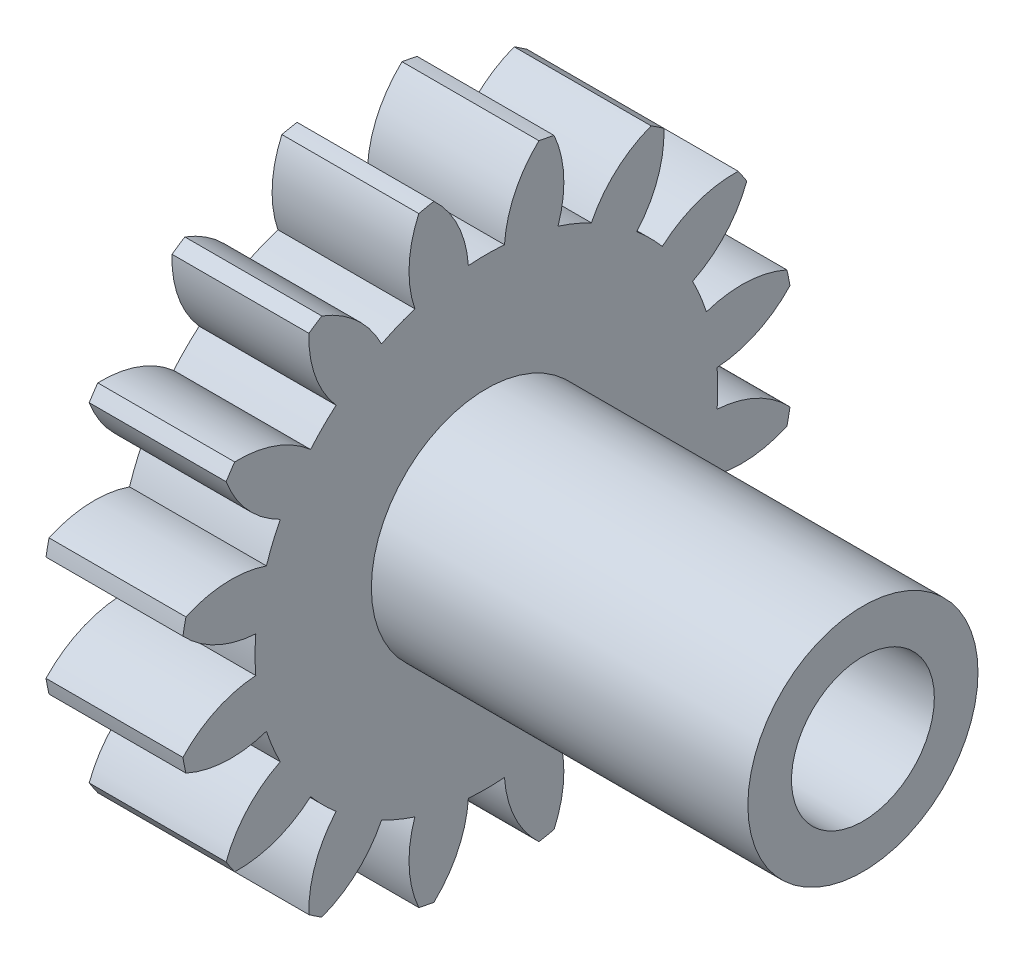
SolidWorks part; units mm, degrees
ref_plane "Plane1" through (0, 0, 0) normal (0, 0, 1) x (1, 0, 0)
ref_plane "Plane2" through (0, 0, 0) normal (0, 1, 0) x (1, 0, 0)
ref_plane "Plane3" through (0, 0, 0) normal (1, 0, 0) x (0, 0, -1)
sketch "HoldingSke" plane through (0, 0, 0) normal (0, 1, 0) x (1, 0, 0)
  line L0 (0, 0) -> (488.3209, -140.0238)
  line L1 (-15, 0) -> (100, 0) construction
  line L2 (0, 0) -> (-2.1039, 2.3779)
  line L3 (0, 0) -> (-11.863, 4.5341)
  line L4 (0, 0) -> (8.3015, 2.3804)
  line L5 (0, 0) -> (-47.5972, -17.7524)
  line L6 (0, 0) -> (-4.2111, -2.8413)
  line L7 (-2.1039, 2.3779) -> (8.8308, 51.9871)
  line L8 (-76.2, 54.61) -> (-74.168, 54.61)
  line L9 (-71.009, 38.7566) -> (-53.1078, 45.2721)
  line L10 (-76.2, 71.12) -> (104.1128, 71.12)
  line L11 (0, 0) -> (-5.08, 0)
  line L12 (-76.2, 101.6) -> (-76.1492, 101.6)
  line L13 (24.9733, 27.94) -> (52.9518, 28.4284)
  line L14 (24.9733, 27.94) -> (25.0241, 27.9398)
  line L15 (24.9733, 27.94) -> (100.4021, 29.52)
  circle A0 centre (0, 0) radius 0.9995
  circle A1 centre (0, 0) radius 8.5852
  circle A2 centre (0, 0) radius 38.1
  circle A3 centre (0, 0) radius 0.9995
  dimension "MHD" = 17.1704
  dimension "Hub_dia" = 76.2
  dimension "Bore" = 1.999
  dimension "MBD" = 1.999
  dimension "Num_teeth" = 16
  dimension "Pitch" = 508
  dimension "Overall_len" = 50.8
  dimension "Show_teeth" = 16
  dimension "Thickness" = 5.08
  dimension "OAL" = 50.8001
  dimension "T_dim" = 2.032
  dimension "Ap" = 20
  dimension "H" = 19.05
  dimension "Pitch_radius" = 180.3128
  dimension "Width" = 5.08
  dimension "Backlash" = 0.0508
  dimension "Addendum_fac" = 1
  dimension "Dedendum_fac" = 1.2
  dimension "Clearance_fac" = 0.2
  dimension "Dedendum_add" = 0.0508
sketch "BasProSke" plane through (0, 0, 0) normal (0, 1, 0) x (1, 0, 0)
  line L0 (-10, 0) -> (60, 0) construction
  line L1 (0, 0) -> (0, 11.43)
  line L2 (0, 0) -> (5.08, 0)
  line L3 (5.08, 0) -> (5.08, 11.43)
  line L4 (5.08, 11.43) -> (0, 11.43)
  dimension "Thickness" = 5.08
  dimension "Diameter" = 22.86
revolve "Base-Revolve" add sketch "BasProSke" angle 360 about L0
sketch "TooCutSke" plane through (0, 0, 0) normal (1, 0, 0) x (0, 0, -1)
  line L1 (0, 0) -> (0, 107) construction
  line L2 (0, 0) -> (-1.0847, 10.1019) construction
  line L3 (0, 0) -> (-3.9484, 19.85) construction
  line L4 (-1.0847, 10.1019) -> (-1.9742, 9.925) construction
  arc A0 (0.6699, 8.559) -> (-0.6699, 8.559) centre (0, 0) ccw
  arc A1 (1.9714, 11.2845) -> (-1.9714, 11.2845) centre (0, 0) ccw
  circle A2 centre (0, 0) radius 10.16 construction
  circle A3 centre (0, 0) radius 9.5473 construction
  arc A4 (-0.6699, 8.559) -> (-1.9714, 11.2845) centre (-4.7253, 8.2959) ccw
  arc A5 (1.9714, 11.2845) -> (0.6699, 8.559) centre (4.7253, 8.2959) ccw
  dimension "Root_dia" = 17.1704
  dimension "Overcut_dia" = 22.9108
  dimension "Pitch_dia" = 20.32
  dimension "Base_dia" = 19.0946
  dimension "Flank_rad" = 4.064
  dimension "Half_ang" = 11.25
  dimension "Half_CT" = 0.907
extrude "ToothCut" cut sketch "TooCutSke" along normal through all
fillet "Breaks" [suppressed] radius 0.0254
fillet "RootFillets" [suppressed] radius 0.3048
pattern_circular "TeethCuts" count 16 every 22.5 about axis through (-10, 0, 0) along (1, 0, 0) of "ToothCut", "RootFillets", "Breaks"
sketch "HubNeaOneSke" plane through (0, 0, 0) normal (-1, 0, 0) x (0, 0, 1)
  circle A0 centre (0, 0) radius 8.5852
  dimension "Diameter" = 17.1704
extrude "HubNearOne" [suppressed] add sketch "HubNeaOneSke" along normal blind 45.7201
sketch "HubNeaBotSke" plane through (0, 0, 0) normal (-1, 0, 0) x (0, 0, 1)
  circle A0 centre (0, 0) radius 8.5852
  dimension "Diameter" = 17.1704
extrude "HubNearBoth" [suppressed] add sketch "HubNeaBotSke" along normal blind 22.86
ref_plane "FarPln" through (5.08, 0, 0) normal (1, 0, 0) x (0, 0, -1)
sketch "HubFarSke" plane through (5.08, 0, 0) normal (1, 0, 0) x (0, 0, -1)
  circle A0 centre (0, 0) radius 8.5852
  dimension "Diameter" = 17.1704
extrude "HubFar" [suppressed] add sketch "HubFarSke" along normal blind 22.86
sketch "BorSke" plane through (0, 0, 0) normal (1, 0, 0) x (0, 0, -1)
  circle A0 centre (0, 0) radius 0.9995
  dimension "Diameter" = 1.999
extrude "Bore" cut sketch "BorSke" along normal mid plane 101.6001
sketch "KeySke" plane through (0, 0, 0) normal (1, 0, 0) x (0, 0, -1)
  line L0 (-0.127, 0) -> (-0.127, 1.0325)
  line L1 (-0.127, 1.0325) -> (0.127, 1.0325)
  line L2 (0.127, 1.0325) -> (0.127, 0)
  line L3 (0, 0) -> (0, 34) construction
  line L4 (-0.127, 0) -> (0.127, 0)
  dimension "Offset" = 1.0325
  dimension "Width" = 0.254
extrude "Keyway" [suppressed] cut sketch "KeySke" along normal mid plane 101.6001
pattern_circular "Keyway2" [suppressed] count 2 every 90 about axis through (-10, 0, 0) along (1, 0, 0)
sketch "Sketch1" plane through (5.08, 0, 0) normal (1, 0, 0) x (0, 0, -1)
  circle A0 centre (0, 0) radius 0.9995
extrude "Boss-Extrude1" add sketch "Sketch1" against normal up to surface (5.08 mm away) up to face at (0, 0, -0.9995)
sketch "Sketch2" plane through (5.08, 0, 0) normal (1, 0, 0) x (0, 0, -1)
  circle A0 centre (0, 0) radius 4.27
  dimension "D1" = 8.54
extrude "Boss-Extrude2" add sketch "Sketch2" along normal blind 13.97
sketch "Sketch3" plane through (19.05, 0, 0) normal (1, 0, 0) x (0, 0, -1)
  circle A0 centre (0, 0) radius 2.65
  dimension "D1" = 5.3
extrude "Cut-Extrude1" cut sketch "Sketch3" against normal blind 3.81
equation "' \"Pitch@HoldingSke\" = 4"
equation "' \"Num_teeth@HoldingSke\" = 12"
equation "' \"Ap@HoldingSke\" =  20"
equation "' \"Ap@HoldingSke\" = 20"
equation "' \"Width@HoldingSke\" = 0.5"
equation "' \"Hub_dia@HoldingSke\"= 1"
equation "' \"Hub_dia@HoldingSke\" = 1"
equation "' \"Overall_len@HoldingSke\" = 1.0"
equation "' \"Bore@HoldingSke\" = 0.75"
equation "' \"T_dim@HoldingSke\" = 0.85"
equation "' \"Width@KeySke\" = 0.25"
equation "' \"Show_teeth@HoldingSke\" = 13"
equation "' \"Backlash@HoldingSke\" = 0.009"
equation "' \"Addendum_fac@HoldingSke\" = 1.0"
equation "' \"Dedendum_fac@HoldingSke\" = 1.25"
equation "' \"Dedendum_add@HoldingSke\" = 0.00005"
equation "' \"Clearance_fac@HoldingSke\" = 0.25"
equation "' \"Pitch@HoldingSke\" = 0.5"
equation "' \"Num_teeth@HoldingSke\" = 23"
equation "' \"Show_teeth@HoldingSke\" = 23"
equation "' \"Backlash@HoldingSke\" = 0.0375"
equation "\"Overcut_dia@TooCutSke\" = (\"Num_teeth@HoldingSke\" + 2 * \"Addendum_fac@HoldingSke\") / \"Pitch@HoldingSke\" + 0.002"
equation "\"Pitch_dia@TooCutSke\" = \"Num_teeth@HoldingSke\" / \"Pitch@HoldingSke\""
equation "\"Base_dia@TooCutSke\" = \"Num_teeth@HoldingSke\" / \"Pitch@HoldingSke\" * cos((\"Ap@HoldingSke\"  * 3.14159265 / 180))"
equation "\"Root_dia@TooCutSke\" = (\"Num_teeth@HoldingSke\" + 2) / \"Pitch@HoldingSke\" - 2 * (\"Addendum_fac@HoldingSke\" + \"Dedendum_fac@HoldingSke\") / \"Pitch@HoldingSke\" - \"Dedendum_add@HoldingSke\" * 2"
equation "\"Half_ang@TooCutSke\" = 180 / \"Num_teeth@HoldingSke\""
equation "\"Half_CT@TooCutSke\" = \"Num_teeth@HoldingSke\" / \"Pitch@HoldingSke\" * sin((3.14159265 / 2 / \"Num_teeth@HoldingSke\")) / 2 - 7 * \"Backlash@HoldingSke\" / 4"
equation "\"Flank_rad@TooCutSke\" = \"Num_teeth@HoldingSke\" / \"Pitch@HoldingSke\" / 5"
equation "\"Radius@RootFillets\" = \"Clearance_fac@HoldingSke\" / \"Pitch@HoldingSke\" + \"Dedendum_add@HoldingSke\""
equation "\"Break_rad@Breaks\" = 0.02 / \"Pitch@HoldingSke\""
equation "\"Thickness@HoldingSke\" = \"Width@HoldingSke\""
equation "\"OAL@HoldingSke\" = \"Thickness@HoldingSke\""
equation "\"MHD@HoldingSke\" = (\"Num_teeth@HoldingSke\" + 2) / \"Pitch@HoldingSke\" - 2 * (\"Addendum_fac@HoldingSke\" + \"Dedendum_fac@HoldingSke\")  / \"Pitch@HoldingSke\" - \"Dedendum_add@HoldingSke\" * 2"
equation "\"MBD@HoldingSke\" = (\"Num_teeth@HoldingSke\" + 2) / \"Pitch@HoldingSke\" - 2 * (\"Addendum_fac@HoldingSke\" + \"Dedendum_fac@HoldingSke\")  / \"Pitch@HoldingSke\" - \"Dedendum_add@HoldingSke\" * 2 - 0.002"
equation "\"MHD@HoldingSke\" = ((sgn( \"MHD@HoldingSke\" - \"Hub_dia@HoldingSke\" )-1)*( \"MHD@HoldingSke\" - \"Hub_dia@HoldingSke\" ))/-2+ \"Hub_dia@HoldingSke\""
equation "\"MBD@HoldingSke\" = ((sgn( \"MBD@HoldingSke\" - \"Bore@HoldingSke\" )-1)*( \"MBD@HoldingSke\" - \"Bore@HoldingSke\" ))/-2+ \"Bore@HoldingSke\""
equation "\"OAL@HoldingSke\" = ((sgn( \"OAL@HoldingSke\" - \"Overall_len@HoldingSke\" )+1)*( \"OAL@HoldingSke\" - \"Overall_len@HoldingSke\" ))/2 + \"Overall_len@HoldingSke\" + 0.000002"
equation "\"Num_teeth@TeethCuts\" = int( \"Show_teeth@HoldingSke\" ) + 1"
equation "\"Num_teeth@TeethCuts\" = ((sgn( \"Num_teeth@TeethCuts\" - \"Num_teeth@HoldingSke\" )-1)*( \"Num_teeth@TeethCuts\" - \"Num_teeth@HoldingSke\" ))/-2+ \"Num_teeth@HoldingSke\""
equation "\"Num_teeth@TeethCuts\" = ((sgn( \"Num_teeth@TeethCuts\" - 2.0)+1)*( \"Num_teeth@TeethCuts\" - 2.0))/2 +2.0"
equation "\"Angle@TeethCuts\" = 360.0 / \"Num_teeth@HoldingSke\""
equation "\"Diameter@BasProSke\" = (\"Num_teeth@HoldingSke\" + 2 * \"Addendum_fac@HoldingSke\") / \"Pitch@HoldingSke\""
equation "\"Thickness@BasProSke\"  = \"Thickness@HoldingSke\""
equation "' \"Fillet_rad@BasProSke\" =  \"Thickness@HoldingSke\" * 0.05"
equation "' \"Fillet_rad@BasProSke\" = \"Thickness@HoldingSke\" * 0.05"
equation "\"MHD@HoldingSke\" = ((sgn( \"MHD@HoldingSke\" - \"Root_dia@TooCutSke\" )-1)*( \"MHD@HoldingSke\" - \"Root_dia@TooCutSke\" ))/-2+ \"Root_dia@TooCutSke\""
equation "\"Diameter@HubNeaOneSke\" = \"MHD@HoldingSke\""
equation "\"Length@HubNearOne\" = \"OAL@HoldingSke\" - \"Thickness@BasProSke\""
equation "\"Diameter@HubNeaBotSke\" = \"MHD@HoldingSke\""
equation "\"Length@HubNearBoth\" = ( \"OAL@HoldingSke\" - \"Thickness@BasProSke\" ) / 2.0"
equation "\"Thickness@FarPln\" = \"Thickness@BasProSke\""
equation "\"Diameter@HubFarSke\" = \"MHD@HoldingSke\""
equation "\"Length@HubFar\" = ( \"OAL@HoldingSke\" - \"Thickness@BasProSke\" ) / 2.0"
equation "\"Diameter@BorSke\" = \"MBD@HoldingSke\""
equation "\"D1@Bore\" = \"OAL@HoldingSke\" * 2.0"
equation "\"D1@Keyway\" = \"OAL@HoldingSke\" * 2.0"
equation "\"Offset@KeySke\" = \"T_dim@HoldingSke\" - \"MBD@HoldingSke\" / 2.0"
